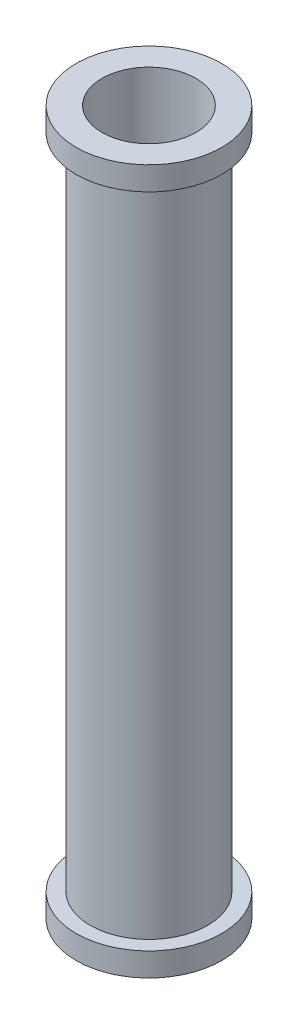
SolidWorks part; units mm, degrees
ref_plane "Front Plane" through (0, 0, 0) normal (0, 0, 1) x (1, 0, 0)
ref_plane "Top Plane" through (0, 0, 0) normal (0, 1, 0) x (1, 0, 0)
ref_plane "Right Plane" through (0, 0, 0) normal (1, 0, 0) x (0, 0, -1)
sketch "Sketch1" plane through (0, 0, 0) normal (0, 0, 1) x (1, 0, 0)
  line L0 (0, 0) -> (0, 1.5)
sketch "Sketch3" plane through (0, 0, 0) normal (0, 1, 0) x (1, 0, 0)
  circle A0 centre (0, 0) radius 0.2
sweep "Sweep-Thin1" add profiles "Sketch3" path "Sketch1" parameters "D1"=0.05
sketch "Sketch5" plane through (0, 0, 0) normal (0, 0, 1) x (1, 0, 0)
  line L0 (0, 0) -> (0, 0.1)
sketch "Sketch6" plane through (0, 0, 0) normal (0, 1, 0) x (1, 0, 0)
  circle A0 centre (0, 0) radius 0.21
sweep "Sweep-Thin2" add profiles "Sketch6" path "Sketch5" parameters "D1"=0.1
mirror "Mirror2" about plane through (0, 1.5, 0) normal (0, 1, 0) of bodies 102
